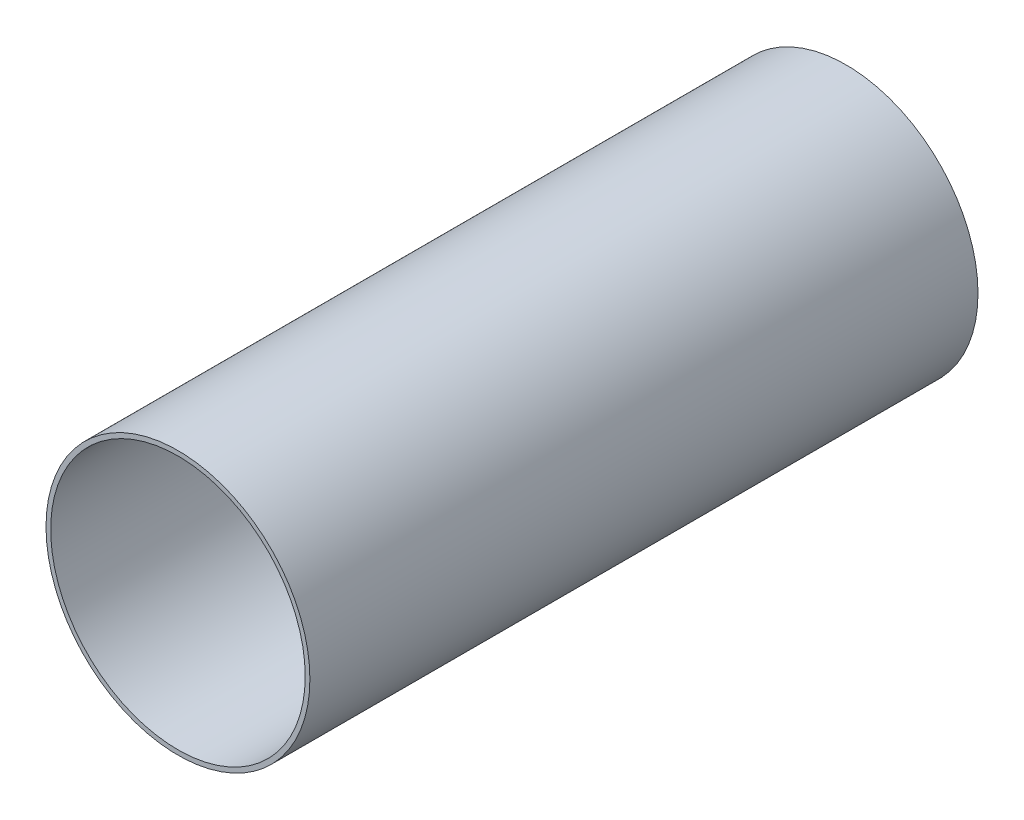
SolidWorks part; units mm, degrees
ref_plane "Front Plane" through (0, 0, 0) normal (0, 0, 1) x (1, 0, 0)
ref_plane "Top Plane" through (0, 0, 0) normal (0, 1, 0) x (1, 0, 0)
ref_plane "Right Plane" through (0, 0, 0) normal (1, 0, 0) x (0, 0, -1)
sketch "Sketch1" plane through (0, 0, 0) normal (0, 0, 1) x (1, 0, 0)
  line L0 (0, 39.5) -> (0, 38.1) construction
  circle A0 centre (0, 0) radius 39.5
  circle A1 centre (0, 0) radius 38.1
  dimension "D1" = 79
  dimension "D2" = 76.2
extrude "Boss-Extrude1" add sketch "Sketch1" along normal blind 200
